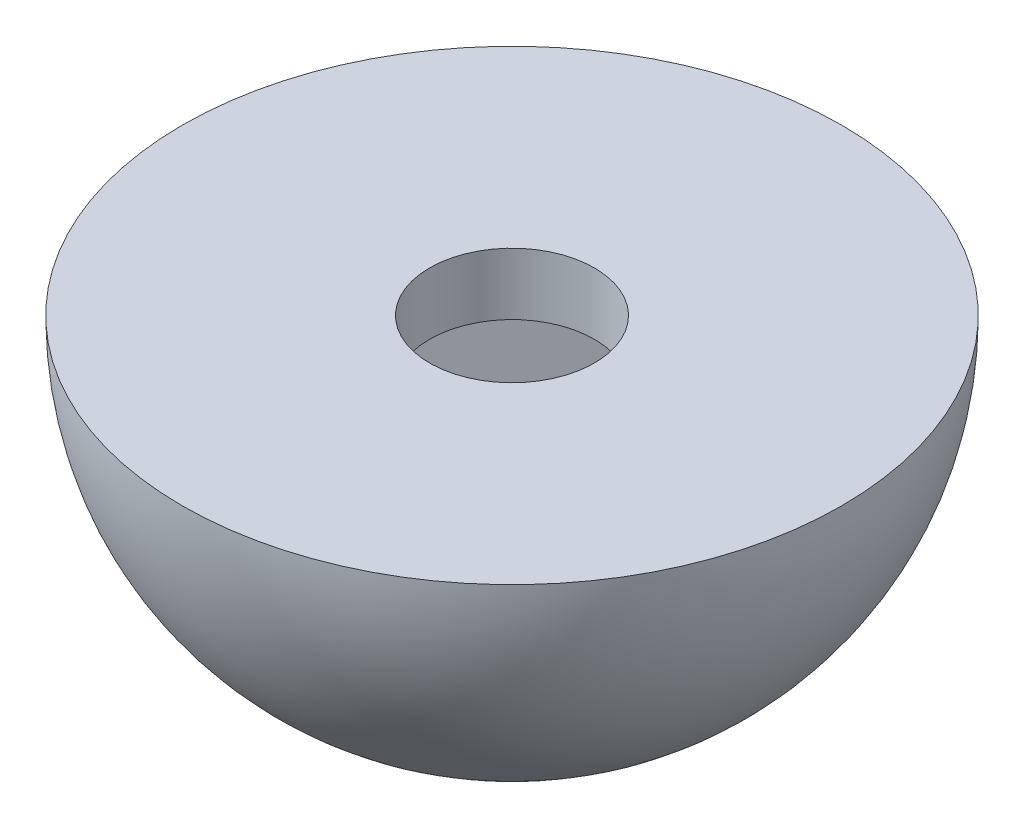
SolidWorks part; units mm, degrees
ref_plane "Plan de face" through (0, 0, 0) normal (0, 0, 1) x (1, 0, 0)
ref_plane "Plan de dessus" through (0, 0, 0) normal (0, 1, 0) x (1, 0, 0)
ref_plane "Plan de droite" through (0, 0, 0) normal (1, 0, 0) x (0, 0, -1)
sketch "Esquisse1" plane through (0, 0, 0) normal (0, 0, 1) x (1, 0, 0)
  line L0 (-4, 0) -> (0, 0)
  line L1 (0, 0) -> (0, -4)
  line L2 (0, -4) -> (-6.4726, -4) construction
  arc A1 (-4, 0) -> (0, -4) centre (0, 0) ccw
  dimension "D1" = 4
  dimension "D2" = 4
revolve "Révolution1" add sketch "Esquisse1" angle 360 about L1
sketch "Esquisse2" plane through (0, 0, 0) normal (0, 1, 0) x (1, 0, 0)
  circle A0 centre (0, 0) radius 1
  dimension "D1" = 2
extrude "Enlèv. mat.-Extru.1" cut sketch "Esquisse2" against normal through all
ref_plane "Plan1" through (0, -3, 0) normal (0, 1, 0) x (1, 0, 0)
sketch "Esquisse4" plane through (0, -3, 0) normal (0, 1, 0) x (1, 0, 0)
  line L1 (2.1673, -0.8553) -> (1.8244, 1.4493)
  line L2 (1.8244, 1.4493) -> (-0.343, 2.3046)
  line L3 (-0.343, 2.3046) -> (-2.1673, 0.8553)
  line L4 (-2.1673, 0.8553) -> (-1.8244, -1.4493)
  line L5 (-1.8244, -1.4493) -> (0.343, -2.3046)
  line L6 (0.343, -2.3046) -> (2.1673, -0.8553)
  circle A0 centre (0, 0) radius 2.0178 construction
  dimension "D1" = 2.33
extrude "Enlèv. mat.-Extru.3" cut sketch "Esquisse4" along normal blind 2.25 and the other way through all
